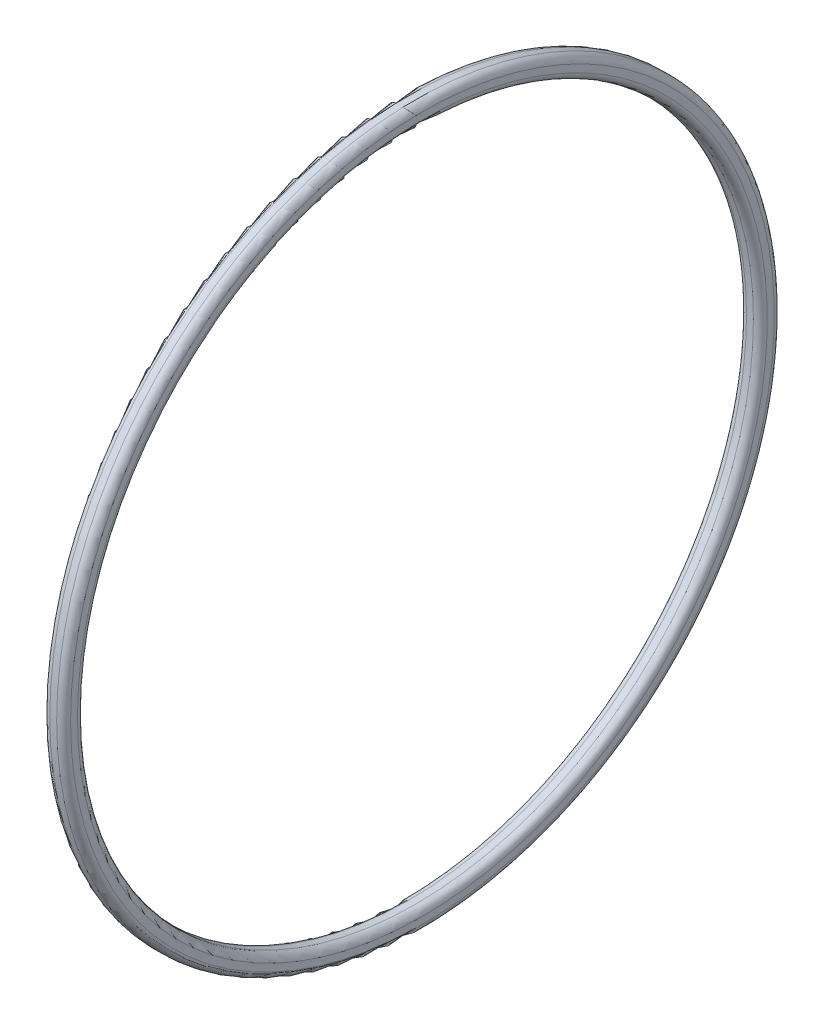
SolidWorks part; units mm, degrees
material "Gomma siliconata"
ref_plane "Piano frontale" through (0, 0, 0) normal (0, 0, 1) x (1, 0, 0)
ref_plane "Piano superiore" through (0, 0, 0) normal (0, 1, 0) x (1, 0, 0)
ref_plane "Piano destro" through (0, 0, 0) normal (1, 0, 0) x (0, 0, -1)
sketch "Schizzo1" plane through (0, 0, 0) normal (0, 0, 1) x (1, 0, 0)
  line L0 (0, 0) -> (55.3578, 0) construction
  line L1 (-0.5, 51.75) -> (0.5, 51.75)
  line L2 (-1.5, 50.75) -> (-1.5, 49.75)
  line L3 (-0.5, 48.75) -> (0.5, 48.75)
  line L4 (1.5, 50.75) -> (1.5, 49.75)
  line L5 (-1.5, 51.75) -> (1.5, 48.75) construction
  line L6 (-1.5, 48.75) -> (1.5, 51.75) construction
  arc A0 (0.5, 51.75) -> (1.5, 50.75) centre (0.5, 50.75) cw
  arc A1 (-1.5, 49.75) -> (-0.5, 48.75) centre (-0.5, 49.75) ccw
  arc A2 (-0.5, 51.75) -> (-1.5, 50.75) centre (-0.5, 50.75) ccw
  arc A3 (0.5, 48.75) -> (1.5, 49.75) centre (0.5, 49.75) ccw
  point P0 (0, 50.25)
  dimension "D3" = 1
  dimension "D1" = 3
  dimension "D2" = 3
  dimension "D4" = 50.25
revolve "Rivoluzione1" add sketch "Schizzo1" angle 360 about L0
